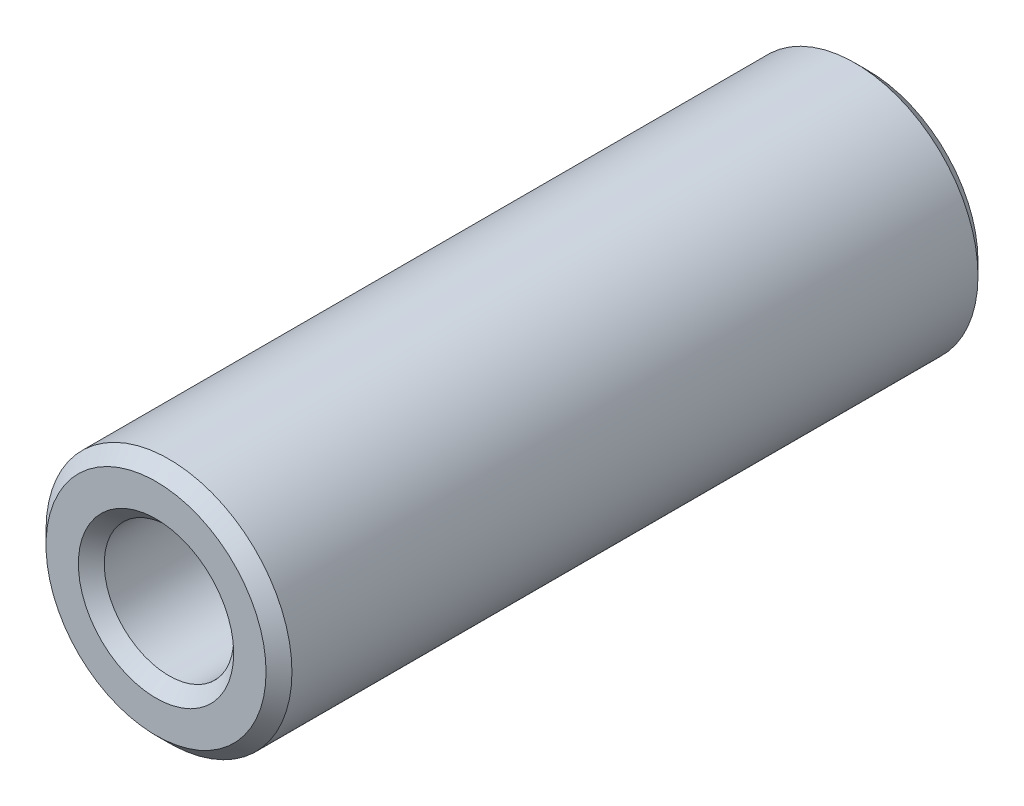
SolidWorks part; units mm, degrees
ref_plane "Спереди" through (0, 0, 0) normal (0, 0, 1) x (1, 0, 0)
ref_plane "Сверху" through (0, 0, 0) normal (0, 1, 0) x (1, 0, 0)
ref_plane "Справа" through (0, 0, 0) normal (1, 0, 0) x (0, 0, -1)
sketch "Эскиз1" plane through (0, 0, 0) normal (0, 0, 1) x (1, 0, 0)
  circle A0 centre (0, 0) radius 5
  circle A1 centre (0, 0) radius 9.5
extrude "Бобышка-Вытянуть1" add sketch "Эскиз1" along normal blind 55
chamfer "Фаска1" distance 1 angle 45 4 edges at (9.5, 0, 0) (9.5, 0, 55) (5, 0, 0) (5, 0, 55)
